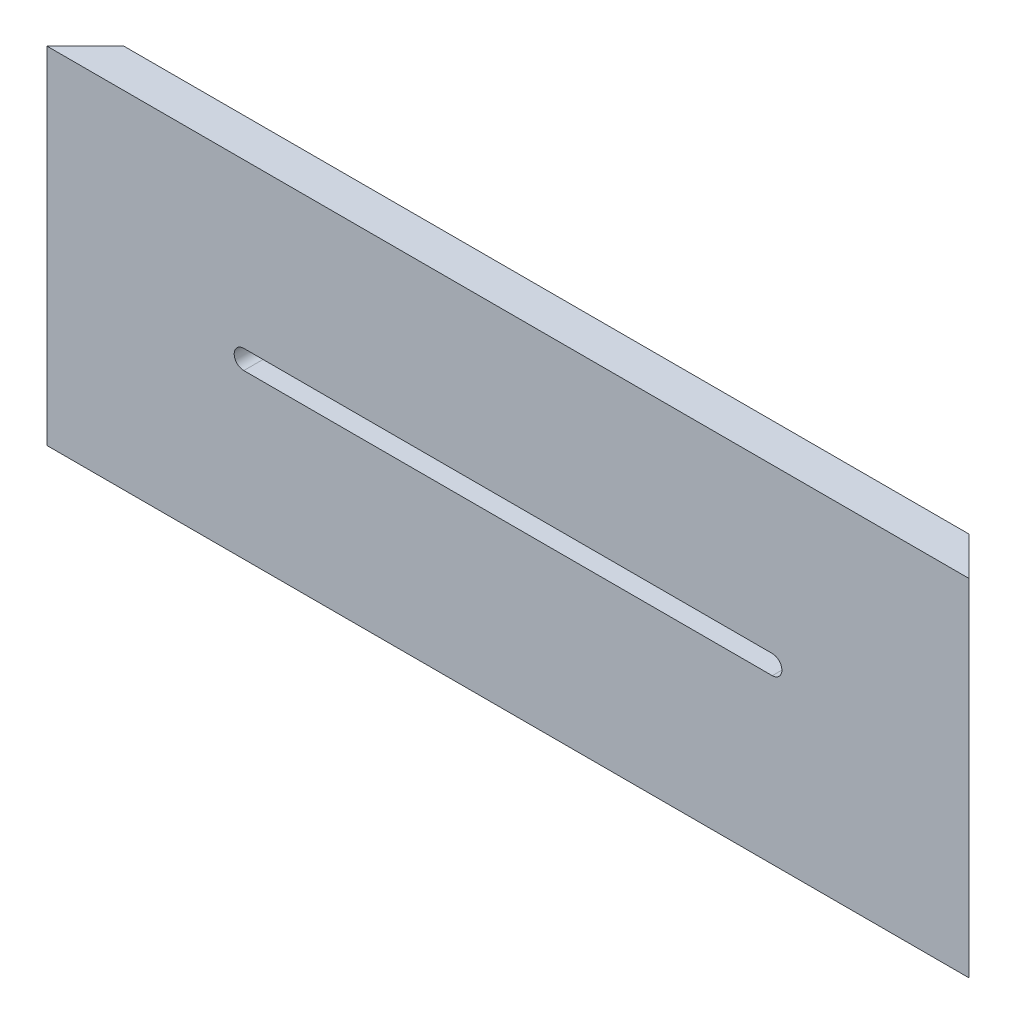
SolidWorks part; units mm, degrees
ref_plane "Front Plane" through (0, 0, 0) normal (0, 0, 1) x (1, 0, 0)
ref_plane "Top Plane" through (0, 0, 0) normal (0, 1, 0) x (1, 0, 0)
ref_plane "Right Plane" through (0, 0, 0) normal (1, 0, 0) x (0, 0, -1)
other "Configuration Table"
sketch "Sketch1" plane through (0, 0, 0) normal (0, 0, 1) x (1, 0, 0)
  line L1 (0, 0) -> (152.4, 0)
  line L2 (0, 0) -> (0, 57.15)
  line L3 (0, 57.15) -> (152.4, 57.15)
  line L4 (152.4, 0) -> (152.4, 57.15)
  dimension "D1" = 57.15
  dimension "D2" = 152.4
extrude "Boss-Extrude1" add sketch "Sketch1" against normal blind 6.35
sketch "Sketch2" plane through (0, 0, 0) normal (0, 0, 1) x (1, 0, 0)
  line L0 (32.5501, 28.575) -> (119.8626, 28.575) construction
  line L1 (32.5501, 30.1625) -> (119.8626, 30.1625)
  line L2 (32.5501, 26.9875) -> (119.8626, 26.9875)
  line L3 (152.4, 0) -> (152.4, 57.15) construction
  line L8 (0, 0) -> (152.4, 0) construction
  arc A0 (32.5501, 30.1625) -> (32.5501, 26.9875) centre (32.5501, 28.575) ccw
  arc A1 (119.8626, 26.9875) -> (119.8626, 30.1625) centre (119.8626, 28.575) ccw
  point P2 (76.2064, 28.575)
  dimension "D4" = 1.5875
  dimension "D1" = 87.3125
  dimension "D2" = 32.5374
  dimension "D3" = 28.575
extrude "Cut-Extrude1" cut sketch "Sketch2" against normal through all
sketch "Sketch3" plane through (0, 57.15, 0) normal (0, 1, 0) x (1, 0, 0)
  line L0 (152.4, 0) -> (146.05, 6.35)
  line L1 (152.4, 6.35) -> (0, 6.35) construction
  line L2 (146.05, 6.35) -> (152.4, 6.35)
  line L3 (152.4, 6.35) -> (152.4, 0)
  line L4 (0, 0) -> (6.35, 6.35)
  line L5 (6.35, 6.35) -> (0, 6.35)
  line L6 (0, 6.35) -> (0, 0)
  dimension "D1" = 45
  dimension "D2" = 45
extrude "Cut-Extrude2" cut sketch "Sketch3" against normal through all
sketch "Sketch4" plane through (0, 0, 0) normal (1, 0, 0) x (0, 0, -1)
  line L0 (6.35, 46.355) -> (3.175, 46.355)
  line L1 (6.35, 0) -> (6.35, 57.15) construction
  line L2 (3.175, 46.355) -> (3.175, 41.5925)
  line L3 (3.175, 41.5925) -> (6.35, 41.5925)
  line L4 (6.35, 41.5925) -> (6.35, 46.355)
  line L5 (6.35, 57.15) -> (0, 57.15) construction
  dimension "D1" = 10.795
  dimension "D2" = 4.7625
  dimension "D3" = 3.175
extrude "Cut-Extrude3" cut sketch "Sketch4" along normal through all
sketch "Sketch5" plane through (0, 0, 0) normal (1, 0, 0) x (0, 0, -1)
  line L0 (6.35, 4.7625) -> (3.175, 4.7625)
  line L1 (6.35, 0) -> (6.35, 41.5925) construction
  line L2 (3.175, 4.7625) -> (3.175, 8.0137)
  line L3 (3.175, 8.0137) -> (6.35, 8.0137)
  line L4 (6.35, 8.0137) -> (6.35, 4.7625)
  line L5 (6.35, 0) -> (0, 0) construction
  dimension "D1" = 4.7625
  dimension "D2" = 3.175
  dimension "D3" = 3.2512
extrude "Cut-Extrude4" cut sketch "Sketch5" along normal through all
sketch "Sketch6" plane through (0, 0, -6.35) normal (0, 0, -1) x (-1, 0, 0)
  line L1 (-146.05, 57.15) -> (-6.35, 57.15) construction
  line L2 (0, 57.15) -> (0, 0) construction
  circle A1 centre (-9.652, 49.911) radius 2.3876
  dimension "D4" = 4.7752
  dimension "D5" = 9.652
  dimension "D6" = 7.239
extrude "Cut-Extrude5" cut sketch "Sketch6" against normal blind 5.08
